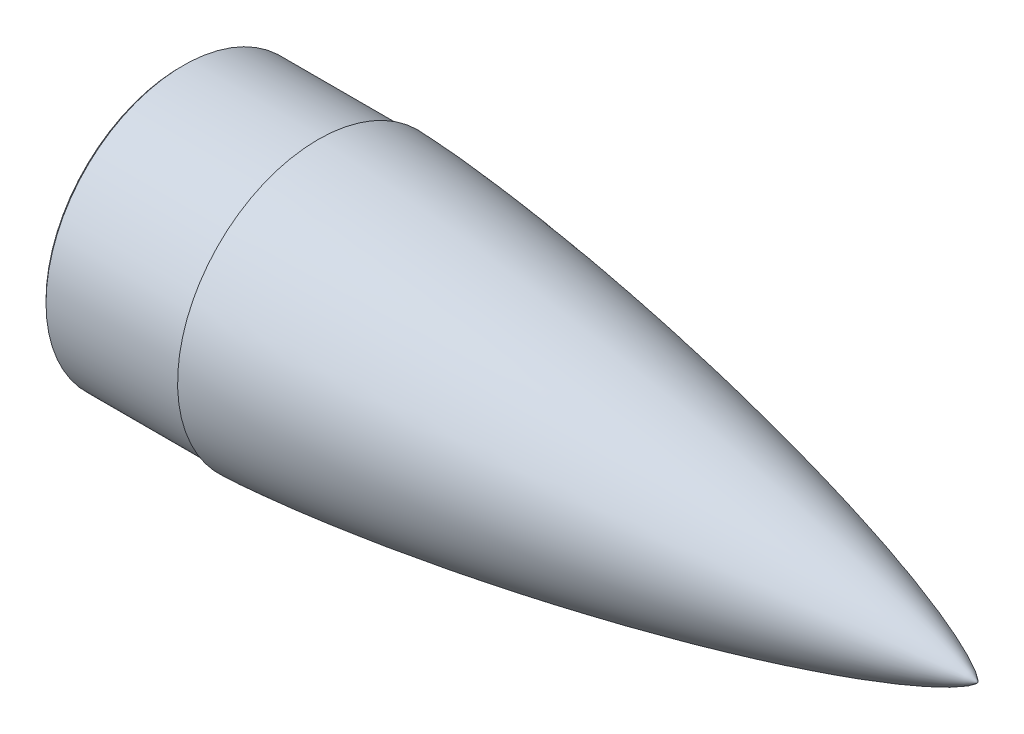
SolidWorks part; units mm, degrees
material "Plain Carbon Steel"
ref_plane "Front Plane" through (0, 0, 0) normal (0, 0, 1) x (1, 0, 0)
ref_plane "Top Plane" through (0, 0, 0) normal (0, 1, 0) x (1, 0, 0)
ref_plane "Right Plane" through (0, 0, 0) normal (1, 0, 0) x (0, 0, -1)
ref_axis "Axis1" through (46.9179, 0, 0) along (-1, 0, 0)
sketch "Sketch10" plane through (0, 0, 0) normal (0, 0, 1) x (1, 0, 0)
  line L1 (-1.0327, 0) -> (486.9547, 0) construction
  line L3 (11.1125, 81.9998) -> (-84.6045, 81.9998)
  line L4 (408.9673, 0) -> (368.9673, 0)
  line L5 (-84.6045, 81.9998) -> (-84.6045, 84.9998)
  line L6 (-84.6045, 84.9998) -> (0.3953, 84.9998)
  line L7 (0.3953, 84.9998) -> (0.3953, 86.9998)
  arc A0 (129.3045, 67.4998) -> (11.1125, 81.9998) centre (-85.3459, -1193.2012) ccw
  spline S0 degree 4 poles (408.9673, 0) (408.9649, 0.0135) (408.958, 0.0399) (408.9365, 0.0905) (408.8922, 0.1741) (408.8263, 0.2756) (408.7217, 0.4158) (408.5611, 0.6051) (408.3056, 0.8724) (407.8697, 1.2753) (407.121, 1.8851) (405.8038, 2.8259) (403.4624, 4.2872) (399.3253, 6.5318) (392.4811, 9.7589) (380.6621, 14.628) (363.6372, 20.7117) (342.2152, 27.4765) (317.4285, 34.4976) (291.8793, 41.1048) (266.2105, 47.229) (240.4455, 52.9334) (214.5989, 58.2554) (188.6809, 63.2176) (165.9462, 67.2533) (146.422, 70.4938) (130.1279, 73.0449) (117.0786, 74.9942) (104.0155, 76.8485) (92.5733, 78.3845) (82.7571, 79.6356) (74.5713, 80.6322) (68.0193, 81.4008) (61.4637, 82.1394) (54.9047, 82.8464) (48.3422, 83.5199) (41.7761, 84.1578) (36.0275, 84.6822) (31.0979, 85.1052) (26.9883, 85.4387) (23.6997, 85.6932) (20.0858, 85.9584) (16.7199, 86.189) (13.6021, 86.387) (10.7327, 86.5546) (8.4366, 86.6787) (6.14, 86.7922) (4.1299, 86.8793) (2.4065, 86.9446) (1.2573, 86.979) (0.6827, 86.9949) (0.3953, 86.9998) knots 0 0 0 0 0 0.00013 0.00026 0.00052 0.0009 0.00128 0.001925 0.002882 0.004418 0.006927 0.011111 0.018279 0.030673 0.051704 0.083102 0.139909 0.202703 0.265496 0.32829 0.391083 0.453877 0.516671 0.579464 0.642258 0.673655 0.705051 0.736448 0.767845 0.799242 0.81494 0.830639 0.846337 0.862036 0.877734 0.893432 0.909131 0.924829 0.932678 0.940527 0.948377 0.956226 0.967169 0.972641 0.978113 0.983585 0.989056 0.994528 0.997264 1 1 1 1 1 construction
  spline S1 degree 4 poles (408.9673, 0) (408.9649, 0.0135) (408.958, 0.0399) (408.9365, 0.0905) (408.8922, 0.1741) (408.8263, 0.2756) (408.7217, 0.4158) (408.5611, 0.6051) (408.3056, 0.8724) (407.8697, 1.2753) (407.121, 1.8851) (405.8038, 2.8259) (403.4624, 4.2872) (399.3253, 6.5318) (392.4811, 9.7589) (380.6621, 14.628) (363.6372, 20.7117) (342.2152, 27.4765) (317.4285, 34.4976) (291.8793, 41.1048) (266.2105, 47.229) (240.4455, 52.9334) (214.5989, 58.2554) (188.6809, 63.2176) (165.9462, 67.2533) (146.422, 70.4938) (130.1279, 73.0449) (117.0786, 74.9942) (104.0155, 76.8485) (92.5733, 78.3845) (82.7571, 79.6356) (74.5713, 80.6322) (68.0193, 81.4008) (61.4637, 82.1394) (54.9047, 82.8464) (48.3422, 83.5199) (41.7761, 84.1578) (36.0275, 84.6822) (31.0979, 85.1052) (26.9883, 85.4387) (23.6997, 85.6932) (20.0858, 85.9584) (16.7199, 86.189) (13.6021, 86.387) (10.7327, 86.5546) (8.4366, 86.6787) (6.14, 86.7922) (4.1299, 86.8793) (2.4065, 86.9446) (1.2573, 86.979) (0.6827, 86.9949) (0.3953, 86.9998) knots 0 0 0 0 0 0.00013 0.00026 0.00052 0.0009 0.00128 0.001925 0.002882 0.004418 0.006927 0.011111 0.018279 0.030673 0.051704 0.083102 0.139909 0.202703 0.265496 0.32829 0.391083 0.453877 0.516671 0.579464 0.642258 0.673655 0.705051 0.736448 0.767845 0.799242 0.81494 0.830639 0.846337 0.862036 0.877734 0.893432 0.909131 0.924829 0.932678 0.940527 0.948377 0.956226 0.967169 0.972641 0.978113 0.983585 0.989056 0.994528 0.997264 1 1 1 1 1
  spline S2 degree 4 poles (368.9673, 0) (368.9653, 0.0123) (368.9594, 0.0365) (368.9406, 0.083) (368.9023, 0.1587) (368.8455, 0.2503) (368.7557, 0.3766) (368.6167, 0.5484) (368.3929, 0.7936) (368.0087, 1.1649) (367.3447, 1.7299) (366.1761, 2.6016) (364.0928, 3.96) (360.426, 6.0407) (354.4022, 9.0183) (344.043, 13.5077) (329.152, 19.1285) (310.4252, 25.3986) (288.7413, 31.9337) (266.3785, 38.1061) (243.9014, 43.8469) (221.332, 49.212) (198.684, 54.2345) (175.9669, 58.9343) (156.0346, 62.7717) (138.9133, 65.8645) (124.6221, 68.3077) (113.1754, 70.1797) (101.7151, 71.9664) (91.6754, 73.4517) (83.0615, 74.6659) (75.8775, 75.6363) (70.1269, 76.3867) (64.3728, 77.1101) (58.6152, 77.8049) (52.854, 78.4695) (47.0892, 79.1019) (42.0417, 79.6247) (37.7129, 80.0488) (34.1039, 80.385) (31.2157, 80.6428) (28.0648, 80.911) (24.6507, 81.1843) (21.4654, 81.4195) (18.5093, 81.6177) (16.0448, 81.767) (14.3191, 81.8612) (12.8395, 81.9336) (11.8527, 81.9739) (11.3593, 81.993) (11.1125, 81.9998) knots 0 0 0 0 0 0.000135 0.00027 0.00054 0.00092 0.001299 0.001947 0.002931 0.004512 0.007081 0.01138 0.018708 0.031424 0.052705 0.084103 0.14091 0.203703 0.266497 0.329291 0.392084 0.454878 0.517672 0.580465 0.643259 0.674656 0.706052 0.737449 0.768846 0.800243 0.815941 0.831639 0.847338 0.863036 0.878735 0.894433 0.910132 0.92583 0.933679 0.941528 0.949378 0.957227 0.96792 0.978613 0.98396 0.989307 0.994653 0.997327 1 1 1 1 1 construction
  spline S3 degree 4 poles (368.9673, 0) (368.9653, 0.0123) (368.9594, 0.0365) (368.9406, 0.083) (368.9023, 0.1587) (368.8455, 0.2503) (368.7557, 0.3766) (368.6167, 0.5484) (368.3929, 0.7936) (368.0087, 1.1649) (367.3447, 1.7299) (366.1761, 2.6016) (364.0928, 3.96) (360.426, 6.0407) (354.4022, 9.0183) (344.043, 13.5077) (329.152, 19.1285) (310.4252, 25.3986) (288.7413, 31.9337) (266.3785, 38.1061) (243.9014, 43.8469) (221.332, 49.212) (198.684, 54.2345) (175.9669, 58.9343) (156.0346, 62.7717) (141.5091, 65.3956) (132.6794, 66.9245) (129.5628, 67.4559) (129.3045, 67.4998) knots 0 0 0 0 0 0.000135 0.00027 0.00054 0.00092 0.001299 0.001947 0.002931 0.004512 0.007081 0.01138 0.018708 0.031424 0.052705 0.084103 0.14091 0.203703 0.266497 0.329291 0.392084 0.454878 0.517672 0.580465 0.643259 0.674656 0.677492 0.677492 0.677492 0.677492 0.677492
  dimension "D1" = 86.9998
  dimension "D2" = 3
  dimension "D3" = 410
  dimension "D4" = 84.9998
  dimension "D5" = 370
  dimension "D6" = 84.9998
revolve "Revolve1" add sketch "Sketch10" angle 360 about axis through (46.9179, 0, 0) along (-1, 0, 0)
chamfer "Chamfer1" distance 1.5 angle 45 1 edges at (-84.6045, 0, -84.9998)
ref_plane "Plane1" through (70, 0, 0) normal (1, 0, 0) x (0, 0, -1)
